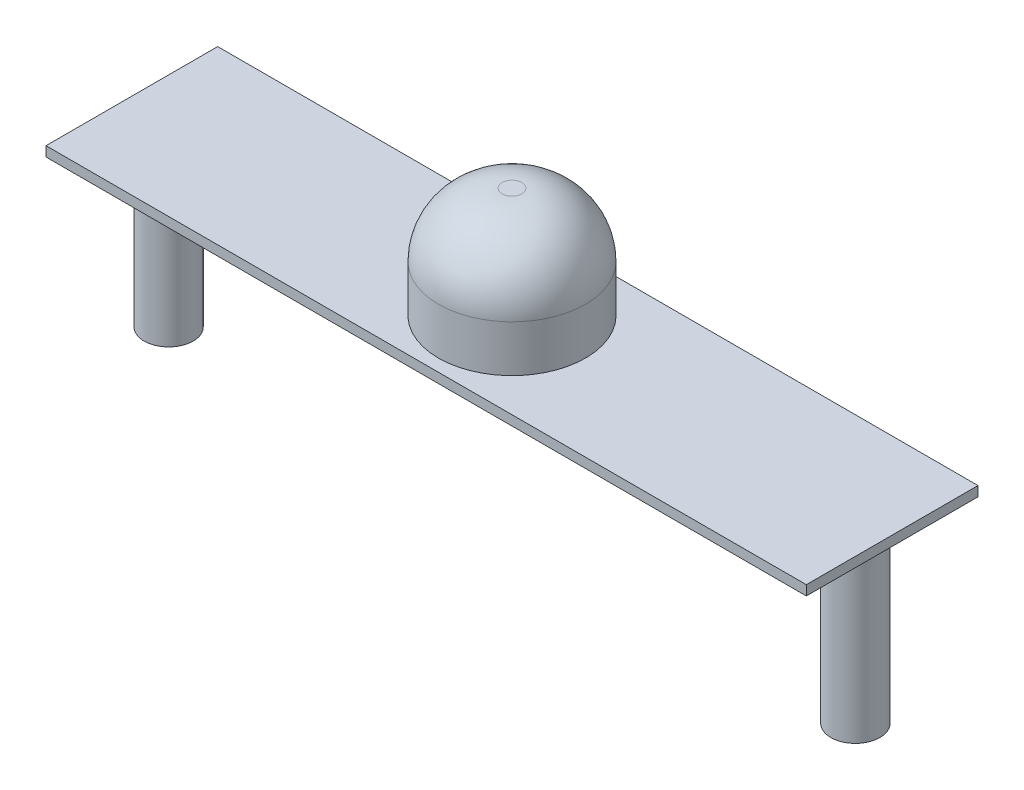
SolidWorks part; units mm, degrees
ref_plane "Front Plane" through (0, 0, 0) normal (0, 0, 1) x (1, 0, 0)
ref_plane "Top Plane" through (0, 0, 0) normal (0, 1, 0) x (1, 0, 0)
ref_plane "Right Plane" through (0, 0, 0) normal (1, 0, 0) x (0, 0, -1)
sketch "Sketch1" plane through (0, 0, 0) normal (0, 1, 0) x (1, 0, 0)
  line L1 (-49.2125, -11.1125) -> (49.2125, -11.1125)
  line L2 (-49.2125, -11.1125) -> (-49.2125, 11.1125)
  line L3 (-49.2125, 11.1125) -> (49.2125, 11.1125)
  line L4 (49.2125, -11.1125) -> (49.2125, 11.1125)
  line L5 (-49.2125, -11.1125) -> (49.2125, 11.1125) construction
  line L6 (-49.2125, 11.1125) -> (49.2125, -11.1125) construction
  point P0 (0, 0)
  dimension "D1" = 98.425
  dimension "D2" = 22.225
extrude "Boss-Extrude1" add sketch "Sketch1" along normal blind 1.27
sketch "Sketch2" plane through (0, 1.27, 0) normal (0, 1, 0) x (1, 0, 0)
  circle A0 centre (0, 0) radius 9.525
extrude "Boss-Extrude2" add sketch "Sketch2" along normal blind 14.2875
fillet "Fillet3" radius 8.255 1 edges at (0, 15.5575, 9.525)
sketch "Sketch3" plane through (0, 0, 0) normal (0, -1, 0) x (1, 0, 0)
  line L0 (0, 0) -> (-44.45, 0) construction
  line L1 (0, 0) -> (0, 5.1123) construction
  circle A0 centre (-44.45, 0) radius 3.175
  circle A1 centre (44.45, 0) radius 3.175
  dimension "D1" = 88.9
extrude "Boss-Extrude3" add sketch "Sketch3" along normal blind 22.225
